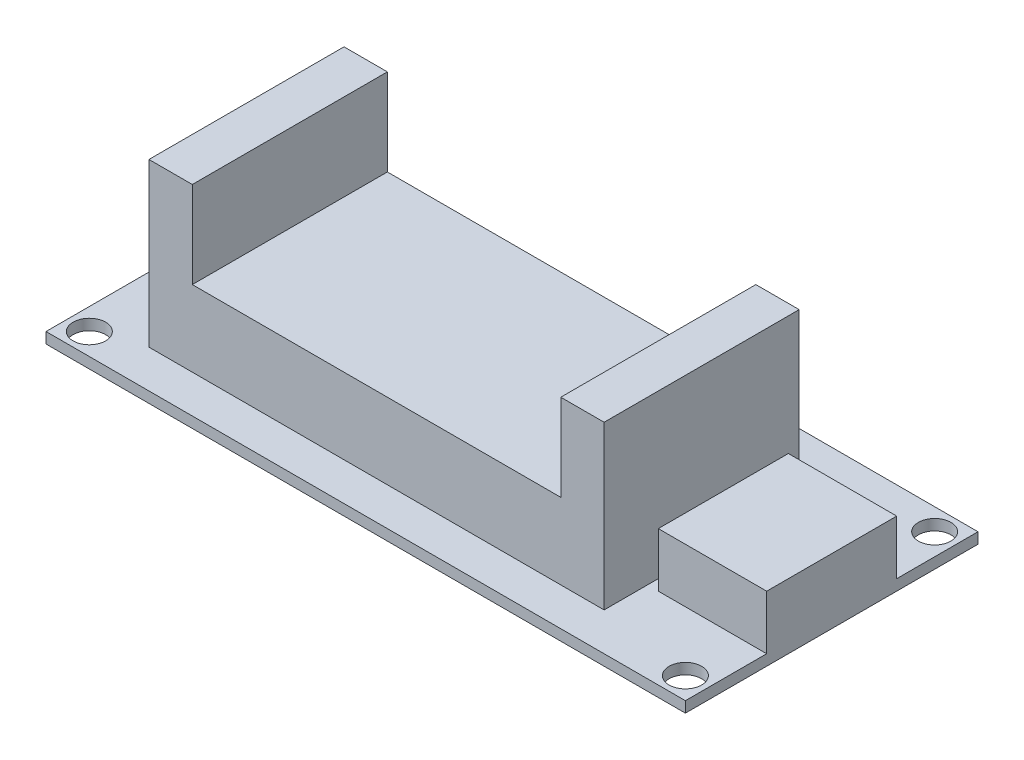
SolidWorks part; units mm, degrees
ref_plane "Front Plane" through (0, 0, 0) normal (0, 0, 1) x (1, 0, 0)
ref_plane "Top Plane" through (0, 0, 0) normal (0, 1, 0) x (1, 0, 0)
ref_plane "Right Plane" through (0, 0, 0) normal (1, 0, 0) x (0, 0, -1)
sketch "Sketch1" plane through (0, 0, 0) normal (0, 1, 0) x (1, 0, 0)
  line L0 (-26.1918, 19.3057) -> (28.8082, 19.3057) construction
  line L1 (-28.1918, 21.3057) -> (30.8082, 21.3057)
  line L2 (-28.1918, 21.3057) -> (-28.1918, -5.6943)
  line L3 (-28.1918, -5.6943) -> (30.8082, -5.6943)
  line L4 (30.8082, 21.3057) -> (30.8082, -5.6943)
  line L5 (28.8082, 19.3057) -> (28.8082, -3.6943) construction
  line L8 (28.8082, -3.6943) -> (-26.1918, -3.6943) construction
  line L9 (-26.1918, -3.6943) -> (-26.1918, 19.3057) construction
  circle A0 centre (-26.1918, -3.6943) radius 1.5
  circle A1 centre (-26.1918, 19.3057) radius 1.5
  circle A2 centre (28.8082, 19.3057) radius 1.5
  circle A3 centre (28.8082, -3.6943) radius 1.5
  dimension "D3" = 23
  dimension "D4" = 55
  dimension "D5" = 2
  dimension "D6" = 2
  dimension "D1" = 59
  dimension "D2" = 27
extrude "Boss-Extrude1" add sketch "Sketch1" along normal blind 1
sketch "Sketch2" plane through (0, 1, 0) normal (0, 1, 0) x (1, 0, 0)
  line L0 (-28.1918, 21.3057) -> (-28.1918, -5.6943) construction
  line L1 (-18.1918, 15.8057) -> (15.8082, 15.8057)
  line L2 (-18.1918, 15.8057) -> (-18.1918, -2.1943)
  line L3 (-18.1918, -2.1943) -> (15.8082, -2.1943)
  line L4 (15.8082, 15.8057) -> (15.8082, -2.1943)
  line L5 (30.8082, 21.3057) -> (-28.1918, 21.3057) construction
  dimension "D1" = 18
  dimension "D2" = 34
  dimension "D3" = 10
  dimension "D4" = 5.5
extrude "Boss-Extrude2" add sketch "Sketch2" along normal blind 7
sketch "Sketch3" plane through (0, 1, 0) normal (0, 1, 0) x (1, 0, 0)
  line L1 (-18.1918, 15.8057) -> (-22.1918, 15.8057)
  line L2 (-18.1918, 15.8057) -> (-18.1918, -2.1943)
  line L3 (-18.1918, -2.1943) -> (-22.1918, -2.1943)
  line L4 (-22.1918, 15.8057) -> (-22.1918, -2.1943)
  point P5 (-18.1918, -2.1943)
  dimension "D1" = 4
extrude "Boss-Extrude3" add sketch "Sketch3" along normal blind 15
sketch "Sketch4" plane through (0, 1, 0) normal (0, 1, 0) x (1, 0, 0)
  line L1 (15.8082, 15.8057) -> (19.8082, 15.8057)
  line L2 (15.8082, 15.8057) -> (15.8082, -2.1943)
  line L3 (15.8082, -2.1943) -> (19.8082, -2.1943)
  line L4 (19.8082, 15.8057) -> (19.8082, -2.1943)
  dimension "D1" = 4
extrude "Boss-Extrude4" add sketch "Sketch4" along normal blind 15
sketch "Sketch7" plane through (0, 1, 0) normal (0, 1, 0) x (1, 0, 0)
  line L0 (30.8082, -5.6943) -> (30.8082, 21.3057) construction
  line L1 (20.8082, 13.8057) -> (30.8082, 13.8057)
  line L2 (20.8082, 13.8057) -> (20.8082, 1.8057)
  line L3 (20.8082, 1.8057) -> (30.8082, 1.8057)
  line L4 (30.8082, 13.8057) -> (30.8082, 1.8057)
  line L5 (-28.1918, -5.6943) -> (30.8082, -5.6943) construction
  dimension "D1" = 10
  dimension "D2" = 12
  dimension "D3" = 7.5
extrude "Boss-Extrude7" add sketch "Sketch7" along normal blind 5
sketch "Sketch8" plane through (0, 1, 0) normal (0, 1, 0) x (1, 0, 0)
  line L0 (-28.1918, 21.3057) -> (-28.1918, -5.6943) construction
  line L1 (-28.1918, 11.2307) -> (-22.1918, 11.2307)
  line L2 (-28.1918, 11.2307) -> (-28.1918, 4.3807)
  line L3 (-28.1918, 4.3807) -> (-22.1918, 4.3807)
  line L4 (-22.1918, 11.2307) -> (-22.1918, 4.3807)
  line L5 (-22.1918, 15.8057) -> (-22.1918, -2.1943) construction
  line L6 (-28.1918, -5.6943) -> (30.8082, -5.6943) construction
  dimension "D1" = 6.85
  dimension "D2" = 10.075
extrude "Boss-Extrude8" add sketch "Sketch8" along normal blind 1.8
